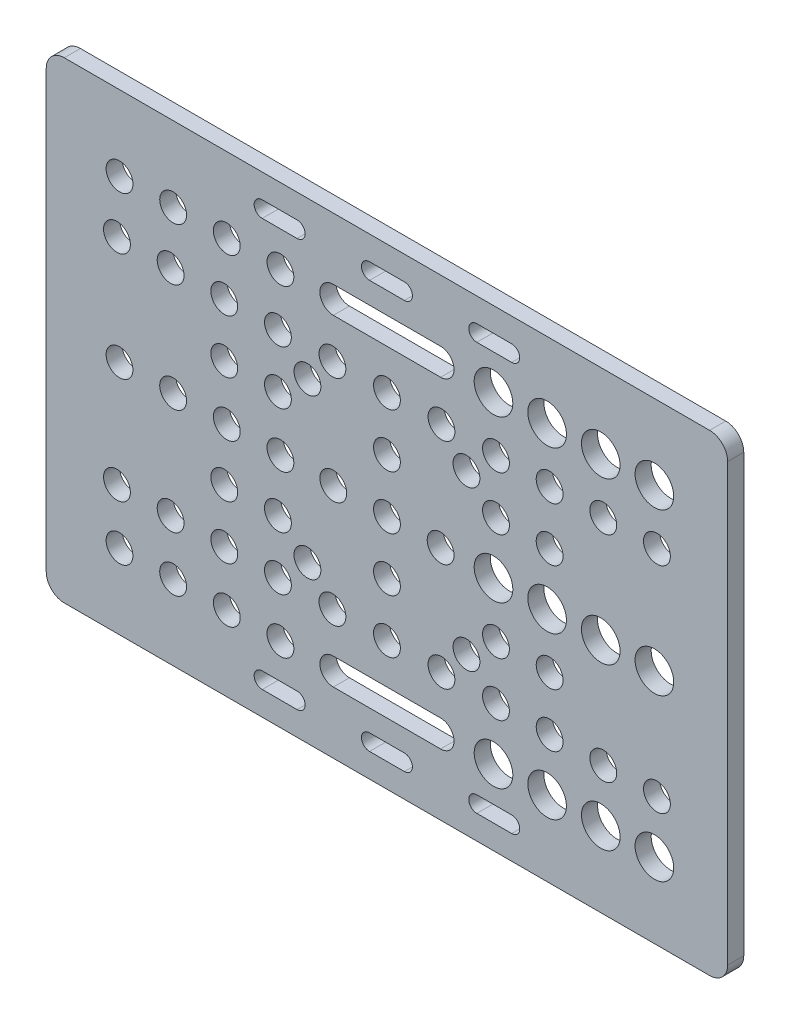
SolidWorks part; units mm, degrees
material "6063-T6"
ref_plane "Front" through (0, 0, 0) normal (0, 0, 1) x (1, 0, 0)
ref_plane "Top" through (0, 0, 0) normal (0, 1, 0) x (1, 0, 0)
ref_plane "Right" through (0, 0, 0) normal (1, 0, 0) x (0, 0, -1)
sketch "Sketch1" plane through (0, 0, 0) normal (0, 0, 1) x (1, 0, 0)
  line L0 (-60.14, 44) -> (-63.5, 40.64) construction
  line L1 (-60.14, -44) -> (60.14, -44)
  line L2 (-63.5, -40.64) -> (-63.5, 40.64)
  line L3 (-60.14, 44) -> (60.14, 44)
  line L4 (63.5, -40.64) -> (63.5, 40.64)
  line L5 (-62.924, -42.5213) -> (62.924, 42.5213) construction
  line L6 (-62.924, 42.5213) -> (62.924, -42.5213) construction
  line L7 (60.14, 44) -> (63.5, 40.64) construction
  line L8 (63.5, -40.64) -> (60.14, -44) construction
  line L9 (-63.5, -40.64) -> (-60.14, -44) construction
  line L10 (-63.5, 0) -> (63.5, 0) construction
  line L11 (0, 44) -> (0, -44) construction
  line L12 (-63.5, -30) -> (63.5, -30) construction
  line L13 (-10, -30) -> (10, -30) construction
  line L14 (-10, -27.5) -> (10, -27.5)
  line L15 (-10, -32.5) -> (10, -32.5)
  line L16 (-10, 30) -> (10, 30) construction
  line L17 (-10, 27.5) -> (10, 27.5)
  line L18 (-10, 32.5) -> (10, 32.5)
  line L19 (-63.5, -38.02) -> (63.5, -38.02) construction
  line L20 (-3.25, -38.02) -> (3.25, -38.02) construction
  line L21 (-3.25, -36.52) -> (3.25, -36.52)
  line L22 (-3.25, -39.52) -> (3.25, -39.52)
  line L23 (-23.25, -38.02) -> (-16.75, -38.02) construction
  line L24 (-23.25, -36.52) -> (-16.75, -36.52)
  line L25 (-23.25, -39.52) -> (-16.75, -39.52)
  line L26 (23.25, -38.02) -> (16.75, -38.02) construction
  line L27 (23.25, -36.52) -> (16.75, -36.52)
  line L28 (23.25, -39.52) -> (16.75, -39.52)
  line L29 (-23.25, 38.02) -> (-16.75, 38.02) construction
  line L30 (-23.25, 36.52) -> (-16.75, 36.52)
  line L31 (-23.25, 39.52) -> (-16.75, 39.52)
  line L32 (-3.25, 38.02) -> (3.25, 38.02) construction
  line L33 (-3.25, 36.52) -> (3.25, 36.52)
  line L34 (-3.25, 39.52) -> (3.25, 39.52)
  line L35 (23.25, 38.02) -> (16.75, 38.02) construction
  line L36 (23.25, 36.52) -> (16.75, 36.52)
  line L37 (23.25, 39.52) -> (16.75, 39.52)
  line L38 (-63.5, -20) -> (63.5, -20) construction
  line L39 (-63.5, -10) -> (63.5, -10) construction
  line L40 (-63.5, -14.82) -> (63.5, -14.82) construction
  arc A0 (-60.14, 44) -> (-63.5, 40.64) centre (-60.14, 40.64) ccw
  arc A1 (63.5, 40.64) -> (60.14, 44) centre (60.14, 40.64) ccw
  arc A2 (60.14, -44) -> (63.5, -40.64) centre (60.14, -40.64) ccw
  arc A3 (-63.5, -40.64) -> (-60.14, -44) centre (-60.14, -40.64) ccw
  circle A4 centre (0, 0) radius 2.5
  circle A5 centre (-49.845, 0) radius 2.5
  circle A6 centre (49.845, 0) radius 3.6
  circle A7 centre (-19.855, -30) radius 2.5
  circle A8 centre (19.855, -30) radius 3.6
  circle A9 centre (-29.85, -30) radius 2.5
  circle A10 centre (-39.85, -30) radius 2.5
  circle A11 centre (-49.845, -30) radius 2.5
  circle A12 centre (49.845, -30) radius 3.6
  circle A13 centre (39.85, -30) radius 3.6
  circle A14 centre (29.85, -30) radius 3.6
  circle A15 centre (49.845, 30) radius 3.6
  circle A16 centre (39.85, 30) radius 3.6
  circle A17 centre (29.85, 30) radius 3.6
  circle A18 centre (19.855, 30) radius 3.6
  circle A19 centre (-19.855, 30) radius 2.5
  circle A20 centre (-29.85, 30) radius 2.5
  circle A21 centre (-39.85, 30) radius 2.5
  circle A22 centre (-49.845, 30) radius 2.5
  arc A23 (-10, -27.5) -> (-10, -32.5) centre (-10, -30) ccw
  arc A24 (10, -32.5) -> (10, -27.5) centre (10, -30) ccw
  arc A25 (-10, 27.5) -> (-10, 32.5) centre (-10, 30) cw
  arc A26 (10, 32.5) -> (10, 27.5) centre (10, 30) cw
  arc A27 (-3.25, -36.52) -> (-3.25, -39.52) centre (-3.25, -38.02) ccw
  arc A28 (3.25, -39.52) -> (3.25, -36.52) centre (3.25, -38.02) ccw
  arc A29 (-23.25, -36.52) -> (-23.25, -39.52) centre (-23.25, -38.02) ccw
  arc A30 (-16.75, -39.52) -> (-16.75, -36.52) centre (-16.75, -38.02) ccw
  arc A31 (23.25, -36.52) -> (23.25, -39.52) centre (23.25, -38.02) cw
  arc A32 (16.75, -39.52) -> (16.75, -36.52) centre (16.75, -38.02) cw
  arc A33 (-23.25, 36.52) -> (-23.25, 39.52) centre (-23.25, 38.02) cw
  arc A34 (-16.75, 39.52) -> (-16.75, 36.52) centre (-16.75, 38.02) cw
  arc A35 (-3.25, 36.52) -> (-3.25, 39.52) centre (-3.25, 38.02) cw
  arc A36 (3.25, 39.52) -> (3.25, 36.52) centre (3.25, 38.02) cw
  arc A37 (23.25, 36.52) -> (23.25, 39.52) centre (23.25, 38.02) ccw
  arc A38 (16.75, 39.52) -> (16.75, 36.52) centre (16.75, 38.02) ccw
  circle A39 centre (-50.32, -20) radius 2.5
  circle A40 centre (-40.32, -20) radius 2.5
  circle A41 centre (-30.32, -20) radius 2.5
  circle A42 centre (-20.32, -20) radius 2.5
  circle A43 centre (50.32, -20) radius 2.5
  circle A44 centre (40.32, -20) radius 2.5
  circle A45 centre (30.32, -20) radius 2.5
  circle A46 centre (20.32, -20) radius 2.5
  circle A47 centre (50.32, 20) radius 2.5
  circle A48 centre (40.32, 20) radius 2.5
  circle A49 centre (30.32, 20) radius 2.5
  circle A50 centre (20.32, 20) radius 2.5
  circle A51 centre (-20.32, 20) radius 2.5
  circle A52 centre (-30.32, 20) radius 2.5
  circle A53 centre (-40.32, 20) radius 2.5
  circle A54 centre (-50.32, 20) radius 2.5
  circle A55 centre (-39.85, 0) radius 2.5
  circle A56 centre (-29.85, 0) radius 2.5
  circle A57 centre (-19.855, 0) radius 2.5
  circle A58 centre (39.85, 0) radius 3.6
  circle A59 centre (29.85, 0) radius 3.6
  circle A60 centre (19.855, 0) radius 3.6
  circle A61 centre (0, -20) radius 2.5
  circle A62 centre (0, 20) radius 2.5
  circle A63 centre (-10.16, -20) radius 2.5
  circle A64 centre (10.16, -20) radius 2.5
  circle A65 centre (10.16, 20) radius 2.5
  circle A66 centre (-10.16, 20) radius 2.5
  circle A67 centre (-10, 0) radius 2.5
  circle A68 centre (10, 0) radius 2.5
  circle A69 centre (0, -10) radius 2.5
  circle A70 centre (0, 10) radius 2.5
  circle A71 centre (-30.32, -10) radius 2.5
  circle A72 centre (-20.32, -10) radius 2.5
  circle A73 centre (30.32, -10) radius 2.5
  circle A74 centre (20.32, -10) radius 2.5
  circle A75 centre (30.32, 10) radius 2.5
  circle A76 centre (20.32, 10) radius 2.5
  circle A77 centre (-30.32, 10) radius 2.5
  circle A78 centre (-20.32, 10) radius 2.5
  circle A79 centre (-14.82, -14.82) radius 2.5
  circle A80 centre (14.82, -14.82) radius 2.5
  circle A81 centre (14.82, 14.82) radius 2.5
  circle A82 centre (-14.82, 14.82) radius 2.5
  point P0 (0, 0)
  point P64 (0, -30)
  point P71 (0, 30)
  point P80 (0, -38.02)
  point P87 (-20, -38.02)
  point P94 (20, -38.02)
  point P101 (-20, 38.02)
  point P108 (0, 38.02)
  point P115 (20, 38.02)
  point P166 (0, -20)
  dimension "D1" = 3.36
  dimension "D4" = 5
  dimension "D5" = 7.2
  dimension "D7" = 14
  dimension "D11" = 25
  dimension "D14" = 9.5
  dimension "D16" = 10.5
  dimension "D20" = 5
  dimension "D21" = 5
  dimension "D22" = 5
  dimension "D23" = 5
  dimension "D24" = 5
  dimension "D25" = 5.16
  dimension "D26" = 29.18
  dimension "D2" = 88
  dimension "D3" = 127
  dimension "D6" = 39.71
  dimension "D8" = 59.7
  dimension "D9" = 79.7
  dimension "D10" = 99.69
  dimension "D12" = 5
  dimension "D13" = 3
  dimension "D15" = 5.98
  dimension "D17" = 3
  dimension "D18" = 10
  dimension "D19" = 13.18
  dimension "D27" = 14.82
extrude "Boss-Extrude1" add sketch "Sketch1" along normal blind 3
